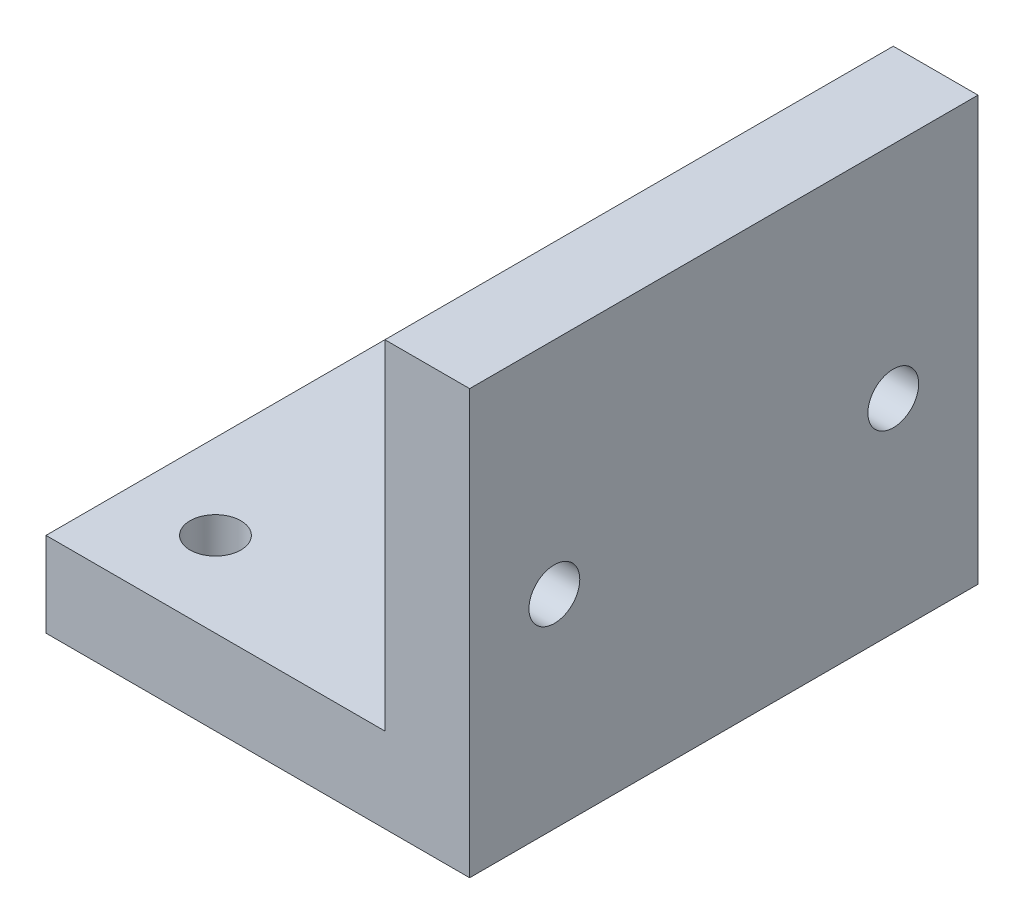
SolidWorks part; units mm, degrees
ref_plane "Alzado" through (0, 0, 0) normal (0, 0, 1) x (1, 0, 0)
ref_plane "Planta" through (0, 0, 0) normal (0, 1, 0) x (1, 0, 0)
ref_plane "Vista lateral" through (0, 0, 0) normal (1, 0, 0) x (0, 0, -1)
sketch "Croquis1" plane through (0, 0, 0) normal (0, 0, 1) x (1, 0, 0)
  line L0 (0, 0) -> (20, 0)
  line L1 (20, 0) -> (20, 20)
  line L2 (20, 20) -> (25, 20)
  line L3 (25, 20) -> (25, -5)
  line L4 (25, -5) -> (0, -5)
  line L5 (0, -5) -> (0, 0)
  dimension "D1" = 5
  dimension "D2" = 5
  dimension "D3" = 25
  dimension "D4" = 25
extrude "Saliente-Extruir1" add sketch "Croquis1" along normal blind 30
sketch "Croquis2" plane through (25, 0, 0) normal (1, 0, 0) x (0, 0, -1)
  line L0 (-15, 20) -> (-15, -5) construction
  line L1 (-30, 20) -> (0, 20) construction
  line L2 (-30, 20) -> (-30, -5) construction
  line L3 (-30, -5) -> (0, -5) construction
  line L4 (0, 20) -> (0, -5) construction
  circle A0 centre (-25, 7) radius 1.5
  circle A1 centre (-5, 7) radius 1.5
  dimension "D1" = 3
  dimension "D2" = 20
  dimension "D3" = 12
extrude "Cortar-Extruir1" cut sketch "Croquis2" against normal blind 30
sketch "Croquis3" plane through (0, -5, 0) normal (0, -1, 0) x (1, 0, 0)
  line L0 (0, 15) -> (25, 15) construction
  line L1 (0, 30) -> (25, 30) construction
  line L2 (0, 30) -> (0, 0) construction
  line L3 (0, 0) -> (25, 0) construction
  line L4 (25, 30) -> (25, 0) construction
  circle A0 centre (5, 5) radius 1.5
  circle A1 centre (5, 25) radius 1.5
  dimension "D2" = 3
  dimension "D1" = 20
  dimension "D3" = 20
extrude "Cortar-Extruir2" cut sketch "Croquis3" against normal blind 30
